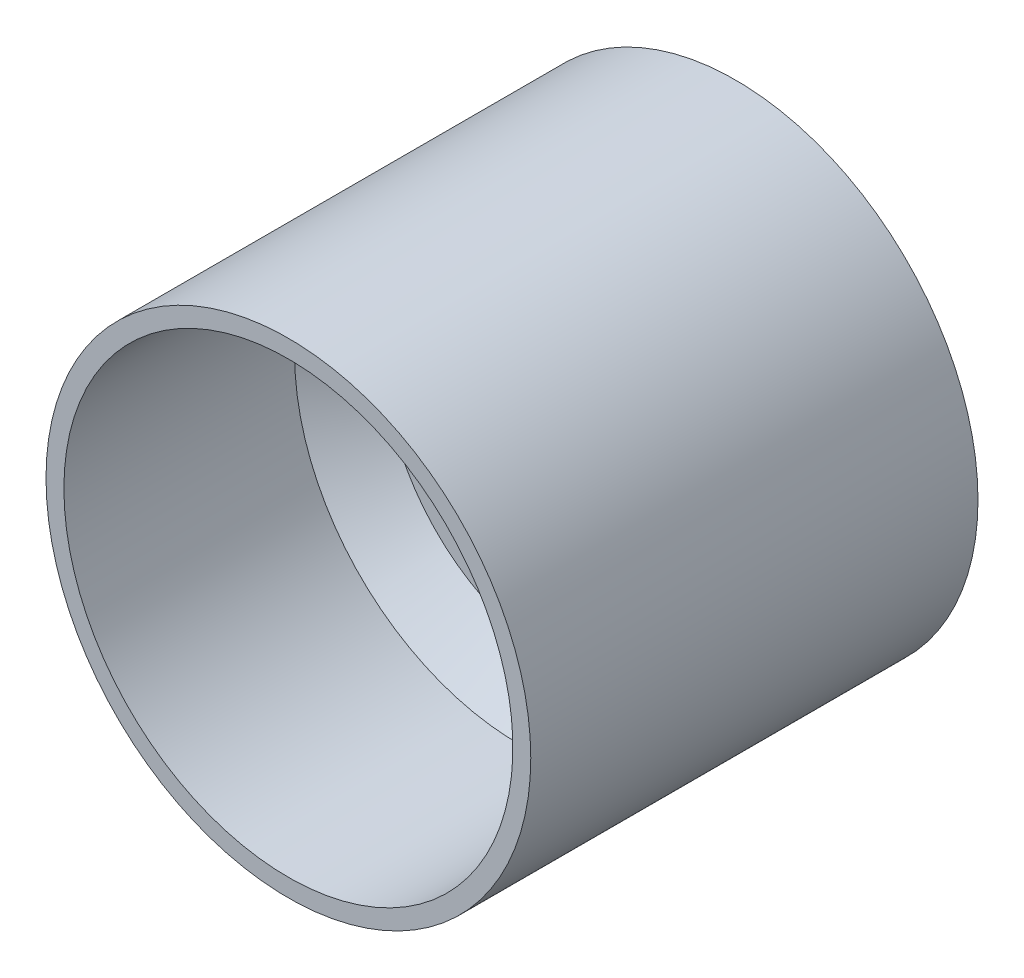
SolidWorks part; units mm, degrees
material "ABS"
ref_plane "Front Plane" through (0, 0, 0) normal (0, 0, 1) x (1, 0, 0)
ref_plane "Top Plane" through (0, 0, 0) normal (0, 1, 0) x (1, 0, 0)
ref_plane "Right Plane" through (0, 0, 0) normal (1, 0, 0) x (0, 0, -1)
sketch "Sketch1" plane through (0, 0, 0) normal (0, 1, 0) x (1, 0, 0)
  line L0 (0, 51.2882) -> (0, -69.4276) construction
  line L1 (15.25, 26.5) -> (15.25, 23.5)
  line L2 (15.25, 23.5) -> (25.1, 23.5)
  line L3 (25.1, 23.5) -> (25.1, -23.5)
  line L4 (25.1, -23.5) -> (27.1, -23.5)
  line L5 (27.1, -23.5) -> (27.1, 26.5)
  line L6 (27.1, 26.5) -> (15.25, 26.5)
  point P9 (25.1, 0)
  dimension "D1" = 30.5
  dimension "D2" = 3
  dimension "D3" = 2
  dimension "D4" = 50.2
  dimension "D6" = 50
revolve "Revolve1" add sketch "Sketch1" angle 360 about L0
sketch "Sketch2" plane through (0, 0, -26.5) normal (0, 0, -1) x (-1, 0, 0)
  circle A0 centre (0, 0) radius 20.25 construction
  circle A1 centre (0, 20.25) radius 2
  circle A2 centre (17.537, -10.125) radius 2
  circle A3 centre (-17.537, -10.125) radius 2
  point P12 (0, 0)
  dimension "D1" = 40.5
  dimension "D2" = 4
  dimension "D3" = 3
extrude "Cut-Extrude1" cut sketch "Sketch2" against normal blind 10
sketch "Sketch3" plane through (0, 0, 0) normal (0, 1, 0) x (1, 0, 0)
  line L0 (25.1, 10.3) -> (0, 10.3)
  line L1 (25.1, 23.5) -> (25.1, -23.5) construction
  line L2 (27.1, 26.5) -> (15.25, 26.5) construction
  line L3 (0, 10.3) -> (0, 7.3)
  line L4 (0, 7.3) -> (25.1, 7.3)
  line L5 (25.1, 7.3) -> (25.1, 10.3)
  line L6 (0, 51.2882) -> (0, -69.4276) construction
  dimension "D1" = 3
  dimension "D2" = 16.2
revolve "Revolve2" add sketch "Sketch3" angle 360 about L0
chamfer "Chamfer1" distance 5 angle 45 2 edges at (-25.1, 0, -7.3) (25.1, 0, -10.3)
sketch "Sketch4" plane through (0, 0, -10.3) normal (0, 0, -1) x (-1, 0, 0)
  line L2 (0, 15.25) -> (0, -15.25) construction
  line L3 (0, 0) -> (0, -84.6003) construction
  line L4 (-25.1, 0) -> (-27.1, 0) construction
  circle A0 centre (0, 0) radius 8.5 construction
  circle A7 centre (0, 0) radius 15.25 construction
  circle A8 centre (0, 12.5) radius 1.5
  circle A9 centre (0, -12.5) radius 1.5
  circle A11 centre (-8.5, 0) radius 1.55
  circle A12 centre (8.5, 0) radius 1.55
  circle A13 centre (0, 0) radius 5.5
  point P21 (0, 0)
  dimension "D1" = 17
  dimension "D2" = 3.1
  dimension "D8" = 3
  dimension "D3" = 11
  dimension "D9" = 12.5
  dimension "D10" = 12.5
  dimension "D11" = 0
extrude "Cut-Extrude2" cut sketch "Sketch4" against normal blind 10
